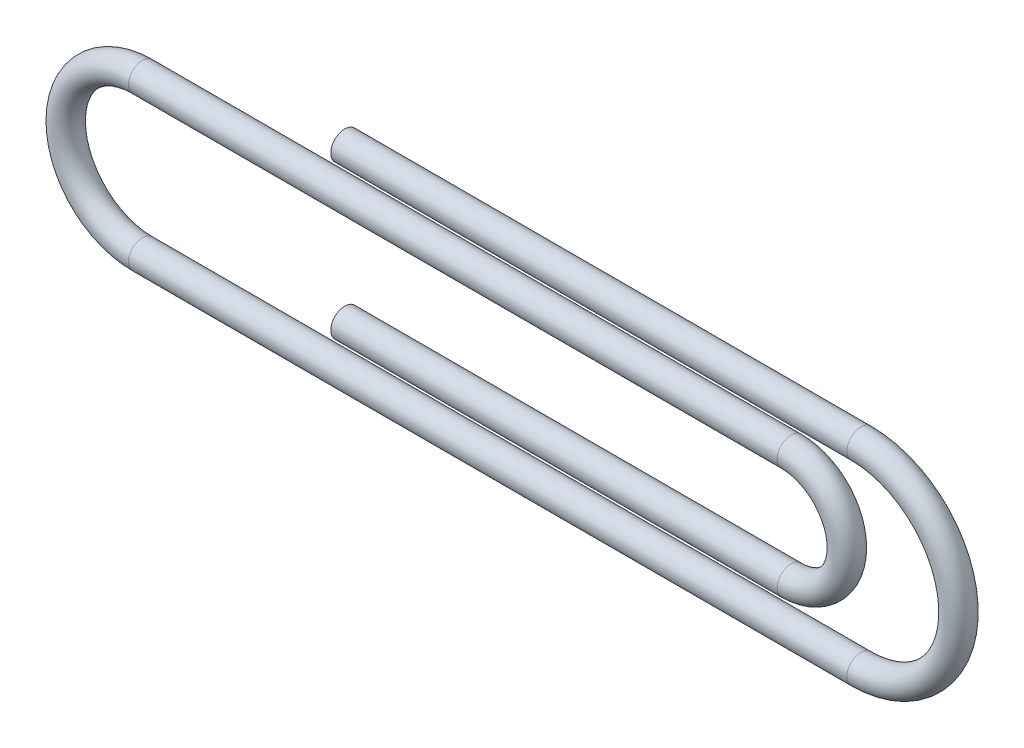
SolidWorks part; units mm, degrees
ref_plane "Front Plane" through (0, 0, 0) normal (0, 0, 1) x (1, 0, 0)
ref_plane "Top Plane" through (0, 0, 0) normal (0, 1, 0) x (1, 0, 0)
ref_plane "Right Plane" through (0, 0, 0) normal (1, 0, 0) x (0, 0, -1)
sketch "Sketch1" plane through (0, 0, 0) normal (0, 0, 1) x (1, 0, 0)
  line L0 (0, 0) -> (18.5, 0)
  line L1 (18.5, -7) -> (-7.25, -7)
  line L2 (-7.25, -1.5) -> (16, -1.5)
  line L3 (16, -5.5) -> (0, -5.5)
  arc A0 (18.5, 0) -> (18.5, -7) centre (18.5, -3.5) cw
  arc A1 (-7.25, -7) -> (-7.25, -1.5) centre (-7.25, -4.25) cw
  arc A2 (16, -1.5) -> (16, -5.5) centre (16, -3.5) cw
  point P11 (0, 0)
  point P13 (8, -5.5)
  point P14 (-10, -4.25)
  point P15 (22, -3.5)
  point P16 (18, -3.5)
  dimension "D1" = 3.5
  dimension "D5" = 32
  dimension "D2" = 1.5
  dimension "D3" = 1.5
  dimension "D4" = 10
  dimension "D6" = 4
  dimension "D7" = 0
sketch "Sketch2" plane through (0, 0, 0) normal (1, 0, 0) x (0, 0, -1)
  circle A0 centre (0, 0) radius 0.5
sweep "Sweep1" add profiles "Sketch2" path "Sketch1"
